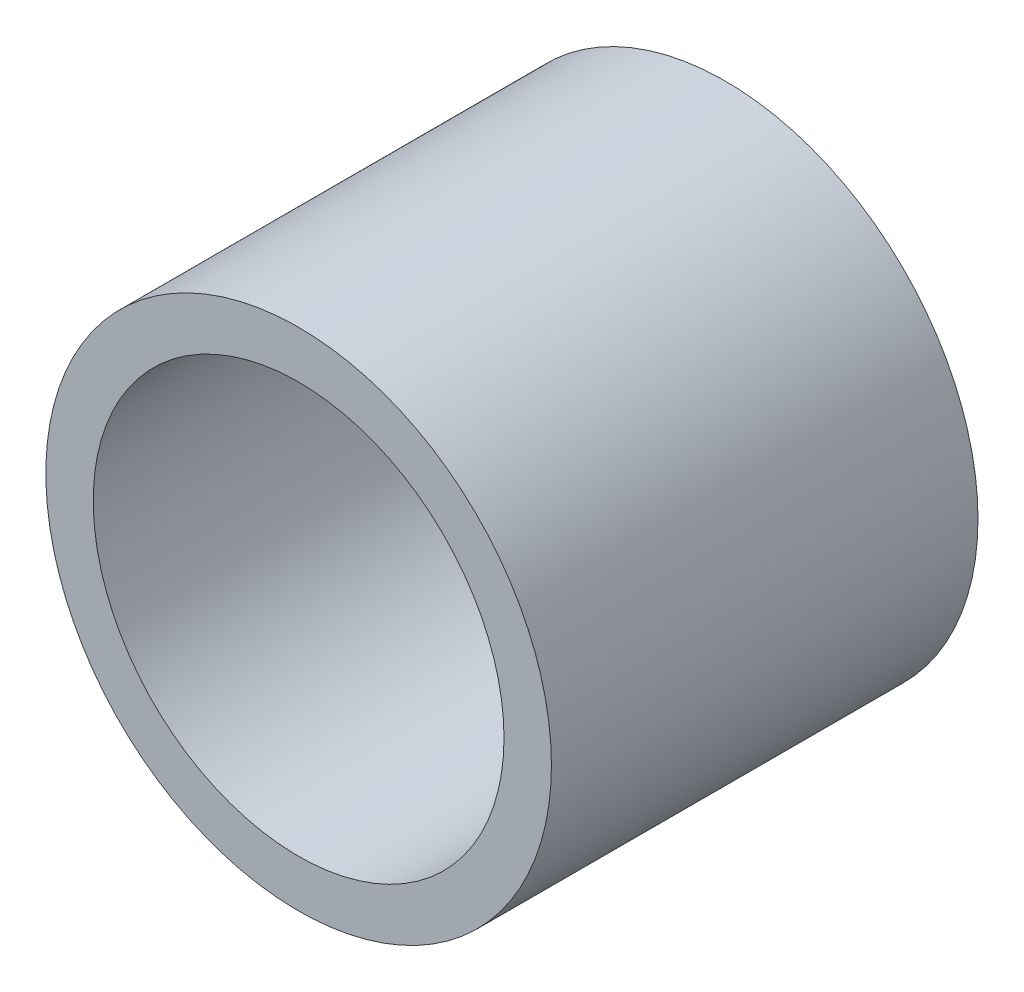
SolidWorks part; units mm, degrees
material "1.0037 (S235JR)"
ref_plane "Front Plane" through (0, 0, 0) normal (0, 0, 1) x (1, 0, 0)
ref_plane "Top Plane" through (0, 0, 0) normal (0, 1, 0) x (1, 0, 0)
ref_plane "Right Plane" through (0, 0, 0) normal (1, 0, 0) x (0, 0, -1)
sketch "Sketch1" plane through (0, 0, 0) normal (0, 0, 1) x (1, 0, 0)
  circle A0 centre (0, 0) radius 16
  circle A1 centre (0, 0) radius 13
  dimension "D1" = 26
  dimension "D2" = 32
extrude "Boss-Extrude1" add sketch "Sketch1" along normal mid plane 27
